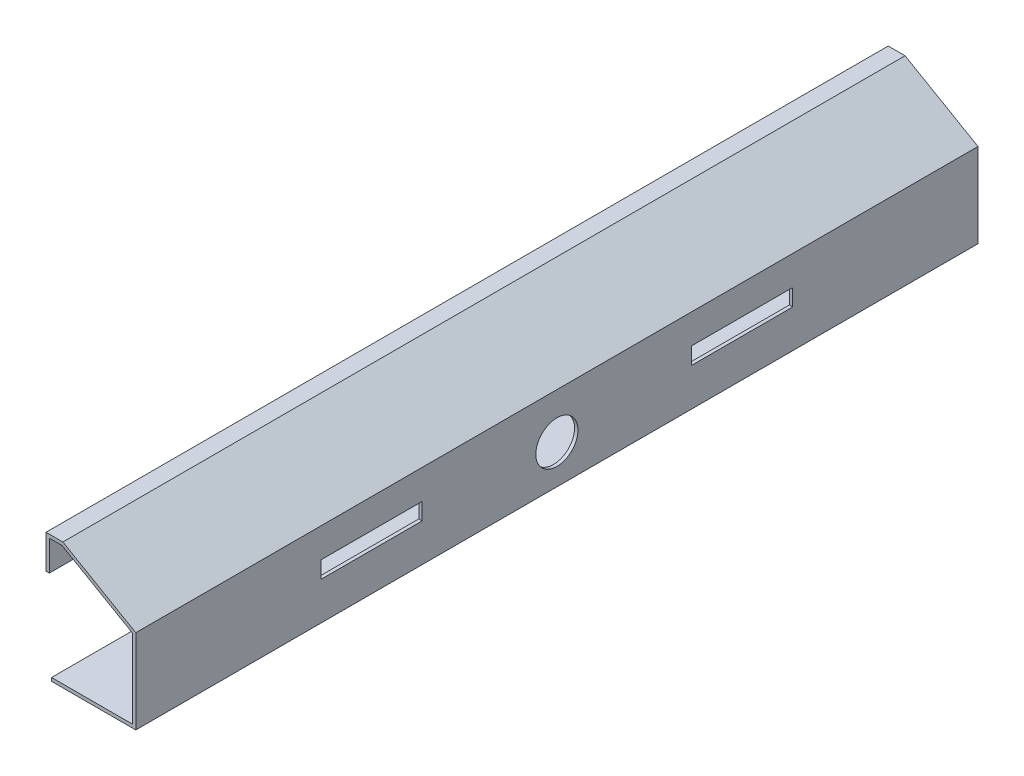
SolidWorks part; units mm, degrees
material "Wrought Stainless Steel"
ref_plane "Front Plane" through (0, 0, 0) normal (0, 0, 1) x (1, 0, 0)
ref_plane "Top Plane" through (0, 0, 0) normal (0, 1, 0) x (1, 0, 0)
ref_plane "Right Plane" through (0, 0, 0) normal (1, 0, 0) x (0, 0, -1)
sketch "Sketch1" plane through (0, 0, 0) normal (0, 0, 1) x (1, 0, 0)
  line L0 (0, 0) -> (-43.3013, 25)
  line L1 (-43.3013, 25) -> (-53.3013, 25)
  line L2 (0, 0) -> (0, -50)
  line L3 (0, -50) -> (-50, -50)
  line L4 (-2, -48) -> (-50, -48)
  line L5 (-2, -1.1547) -> (-2, -48)
  line L6 (-2, -1.1547) -> (-43.8372, 23)
  line L7 (-43.8372, 23) -> (-53.3013, 23)
  line L8 (-53.3013, 25) -> (-53.3013, 23)
  line L9 (-50, -48) -> (-50, -50)
  dimension "D1" = 50
  dimension "D2" = 50
  dimension "D3" = 10
  dimension "D4" = 120
  dimension "D5" = 50
  dimension "D6" = 2
extrude "Boss-Extrude1" add sketch "Sketch1" along normal blind 500
sketch "Sketch2" plane through (0, 0, 0) normal (1, 0, 0) x (0, 0, -1)
  line L0 (-500, -50) -> (0, -50) construction
  line L1 (0, -50) -> (0, 0) construction
  circle A0 centre (-250, -27) radius 12.5
  dimension "D1" = 25
  dimension "D2" = 23
  dimension "D3" = 250
extrude "Cut-Extrude1" cut sketch "Sketch2" against normal through all
sketch "Sketch3" plane through (0, 0, 0) normal (1, 0, 0) x (0, 0, -1)
  line L0 (-250, 0) -> (-250, -50) construction
  line L1 (-500, 0) -> (0, 0) construction
  line L2 (-500, -50) -> (0, -50) construction
  line L3 (-110, -17.5) -> (-170, -17.5)
  line L4 (-390, -27.5) -> (-330, -27.5)
  line L5 (-390, -27.5) -> (-390, -17.5)
  line L6 (-390, -17.5) -> (-330, -17.5)
  line L7 (-330, -27.5) -> (-330, -17.5)
  line L8 (-390, -27.5) -> (-330, -17.5) construction
  line L9 (-390, -17.5) -> (-330, -27.5) construction
  line L10 (-170, -27.5) -> (-170, -17.5)
  line L11 (-110, -27.5) -> (-170, -27.5)
  line L12 (-110, -27.5) -> (-110, -17.5)
  point P6 (-360, -22.5)
  dimension "D1" = 60
  dimension "D2" = 10
  dimension "D3" = 22.5
  dimension "D4" = 80
extrude "Cut-Extrude2" cut sketch "Sketch3" against normal blind 2
sketch "Sketch4" plane through (-53.3013, 0, 0) normal (-1, 0, 0) x (0, 0, 1)
  line L0 (500, 25) -> (0, 25) construction
  line L1 (0, 5) -> (500, 5)
  line L2 (0, 5) -> (0, 25)
  line L3 (0, 25) -> (500, 25)
  line L4 (500, 5) -> (500, 25)
  line L5 (0, 5) -> (500, 25) construction
  line L6 (0, 25) -> (500, 5) construction
  line L7 (0, 23) -> (0, -1.1547) construction
  point P0 (250, 15)
  dimension "D1" = 500
  dimension "D2" = 20
  dimension "D3" = 10
  dimension "D4" = 0
extrude "Boss-Extrude2" add sketch "Sketch4" against normal blind 2
